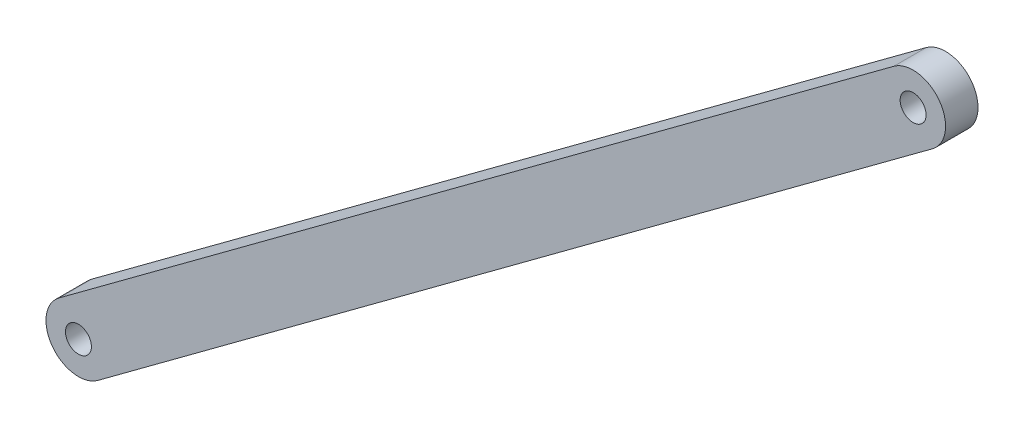
SolidWorks part; units mm, degrees
ref_plane "Front Plane" through (0, 0, 0) normal (0, 0, 1) x (1, 0, 0)
ref_plane "Top Plane" through (0, 0, 0) normal (0, 1, 0) x (1, 0, 0)
ref_plane "Right Plane" through (0, 0, 0) normal (1, 0, 0) x (0, 0, -1)
sketch "Sketch1" plane through (0, 0, 0) normal (0, 0, 1) x (1, 0, 0)
  line L2 (-256.9192, 65.0844) -> (-128.3253, 160.2875) construction
  line L3 (-122.3751, 152.2504) -> (-250.969, 57.0473) construction
  line L4 (-256.9192, 65.0844) -> (-128.3253, 160.2875)
  line L5 (-122.3751, 152.2504) -> (-250.969, 57.0473)
  circle A6 centre (-125.3502, 156.2689) radius 2 construction
  circle A7 centre (-253.9441, 61.0659) radius 2 construction
  arc A8 (-122.3751, 152.2504) -> (-128.3253, 160.2875) centre (-125.3502, 156.2689) ccw construction
  arc A9 (-256.9192, 65.0844) -> (-250.969, 57.0473) centre (-253.9441, 61.0659) ccw construction
  circle A10 centre (-125.3502, 156.2689) radius 2
  circle A11 centre (-253.9441, 61.0659) radius 2
  arc A12 (-122.3751, 152.2504) -> (-128.3253, 160.2875) centre (-125.3502, 156.2689) ccw
  arc A13 (-256.9192, 65.0844) -> (-250.969, 57.0473) centre (-253.9441, 61.0659) ccw
extrude "Boss-Extrude1" add sketch "Sketch1" against normal blind 5 from offset 5
